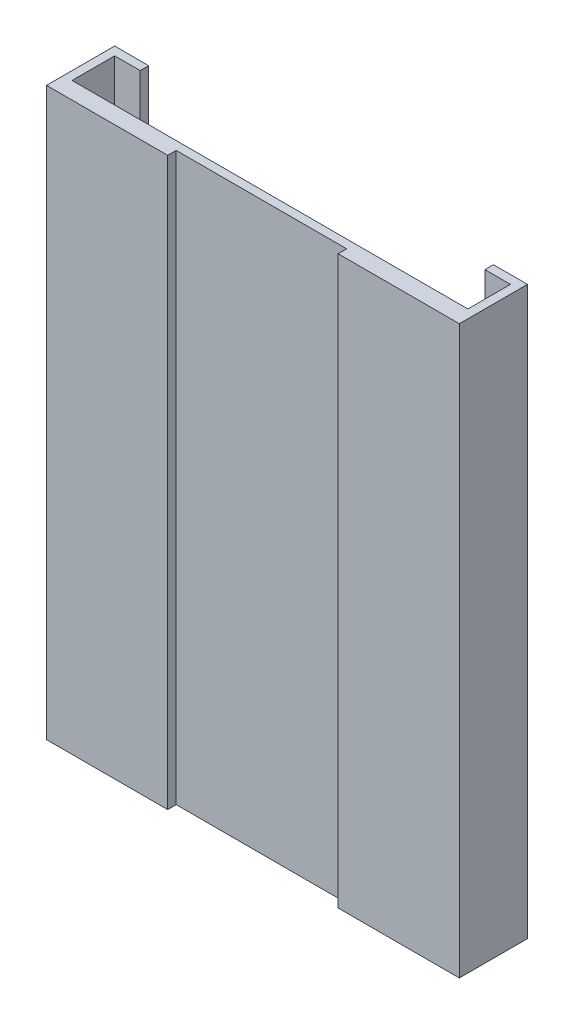
SolidWorks part; units mm, degrees
ref_plane "Front Plane" through (0, 0, 0) normal (0, 0, 1) x (1, 0, 0)
ref_plane "Top Plane" through (0, 0, 0) normal (0, 1, 0) x (1, 0, 0)
ref_plane "Right Plane" through (0, 0, 0) normal (1, 0, 0) x (0, 0, -1)
sketch "Sketch1" plane through (0, 0, 0) normal (0, 0, 1) x (1, 0, 0)
  line L1 (-9.69, 13.3) -> (9.69, 13.3)
  line L2 (-9.69, 13.3) -> (-9.69, -13.3)
  line L3 (-9.69, -13.3) -> (9.69, -13.3)
  line L4 (9.69, 13.3) -> (9.69, -13.3)
  line L5 (-9.69, 13.3) -> (9.69, -13.3) construction
  line L6 (-9.69, -13.3) -> (9.69, 13.3) construction
  point P0 (0, 0)
  dimension "D1" = 19.38
  dimension "D2" = 26.6
extrude "Boss-Extrude1" add sketch "Sketch1" against normal blind 0.8
sketch "Sketch2" plane through (0, 0, -0.8) normal (0, 0, -1) x (-1, 0, 0)
  line L0 (9.69, -13.3) -> (-9.69, -13.3) construction
  line L1 (-9.69, 13.3) -> (-9.29, 13.3)
  line L2 (-9.69, 13.3) -> (-9.69, -13.3)
  line L3 (-9.69, -13.3) -> (-9.29, -13.3)
  line L4 (-9.29, 13.3) -> (-9.29, -13.3)
  dimension "D1" = 0.4
extrude "Boss-Extrude2" add sketch "Sketch2" along normal blind 2.4
sketch "Sketch3" plane through (0, 0, -0.8) normal (0, 0, -1) x (-1, 0, 0)
  line L0 (9.69, -13.3) -> (-9.29, -13.3) construction
  line L1 (9.69, 13.3) -> (9.29, 13.3)
  line L2 (9.69, 13.3) -> (9.69, -13.3)
  line L3 (9.69, -13.3) -> (9.29, -13.3)
  line L4 (9.29, 13.3) -> (9.29, -13.3)
  dimension "D1" = 0.4
extrude "Boss-Extrude3" add sketch "Sketch3" along normal blind 2.4
sketch "Sketch4" plane through (0, -13.3, 0) normal (0, -1, 0) x (1, 0, 0)
  line L1 (-4, 0) -> (4, 0)
  line L2 (-4, 0) -> (-4, -0.4)
  line L3 (-4, -0.4) -> (4, -0.4)
  line L4 (4, 0) -> (4, -0.4)
  line L5 (-9.69, 0) -> (9.69, 0) construction
  point P7 (0, 0)
  point P8 (0, 0)
  dimension "D1" = 0.4
  dimension "D2" = 8
extrude "Cut-Extrude1" cut sketch "Sketch4" against normal through all
sketch "Sketch5" plane through (9.29, 0, 0) normal (-1, 0, 0) x (0, 0, 1)
  line L0 (-3.2, -13.3) -> (-0.8, -13.3) construction
  line L1 (-3.2, 13.3) -> (-2.8, 13.3)
  line L2 (-3.2, 13.3) -> (-3.2, -13.3)
  line L3 (-3.2, -13.3) -> (-2.8, -13.3)
  line L4 (-2.8, 13.3) -> (-2.8, -13.3)
  dimension "D1" = 0.4
extrude "Boss-Extrude4" add sketch "Sketch5" along normal blind 1.2
sketch "Sketch6" plane through (-9.29, 0, 0) normal (1, 0, 0) x (0, 0, -1)
  line L0 (3.2, 13.3) -> (0.8, 13.3) construction
  line L1 (3.2, -13.3) -> (2.8, -13.3)
  line L2 (3.2, -13.3) -> (3.2, 13.3)
  line L3 (3.2, 13.3) -> (2.8, 13.3)
  line L4 (2.8, -13.3) -> (2.8, 13.3)
  dimension "D1" = 0.4
extrude "Boss-Extrude5" add sketch "Sketch6" along normal blind 1.2
sketch "Sketch7" plane through (0, 0, -0.8) normal (0, 0, -1) x (-1, 0, 0)
  line L0 (9.29, 13.3) -> (9.29, -13.3) construction
  line L1 (-9.29, -13.3) -> (9.29, -13.3)
  line L2 (-9.29, -13.3) -> (-9.29, -12.9)
  line L3 (-9.29, -12.9) -> (9.29, -12.9)
  line L4 (9.29, -13.3) -> (9.29, -12.9)
  dimension "D1" = 0.4
extrude "Boss-Extrude6" add sketch "Sketch7" along normal through all
sketch "Sketch8" plane through (0, 0, -0.8) normal (0, 0, -1) x (-1, 0, 0)
  line L0 (-9.29, 13.3) -> (9.29, 13.3) construction
  line L1 (-5.445, 13.3) -> (-3.445, 13.3)
  line L2 (-5.445, 13.3) -> (-5.445, 12.5)
  line L3 (-5.445, 12.5) -> (-3.445, 12.5)
  line L4 (-3.445, 13.3) -> (-3.445, 12.5)
  point P6 (-4.445, 13.3)
  dimension "D1" = 0.8
  dimension "D2" = 2
  dimension "D3" = 4.845
extrude "Boss-Extrude7" add sketch "Sketch8" along normal blind 0.8
sketch "Sketch9" plane through (0, 0, -0.8) normal (0, 0, -1) x (-1, 0, 0)
  line L0 (-3.445, 13.3) -> (9.29, 13.3) construction
  line L1 (3.3215, 13.3) -> (5.5685, 13.3)
  line L2 (3.3215, 13.3) -> (3.3215, 12.5)
  line L3 (3.3215, 12.5) -> (5.5685, 12.5)
  line L4 (5.5685, 13.3) -> (5.5685, 12.5)
  point P6 (4.445, 13.3)
  dimension "D1" = 0.8
  dimension "D2" = 4.845
extrude "Boss-Extrude8" add sketch "Sketch9" along normal blind 0.8
sketch "Sketch10" plane through (-5.5685, 0, 0) normal (-1, 0, 0) x (0, 0, 1)
  line L0 (-1.6, 12.5) -> (-0.8, 13.3)
  line L1 (-0.8, 13.3) -> (-1.6, 13.3)
  line L2 (-1.6, 13.3) -> (-1.6, 12.5)
extrude "Cut-Extrude2" cut sketch "Sketch10" against normal up to surface (11.0135 mm away) up to face at (5.445, 12.9, -1.2)
